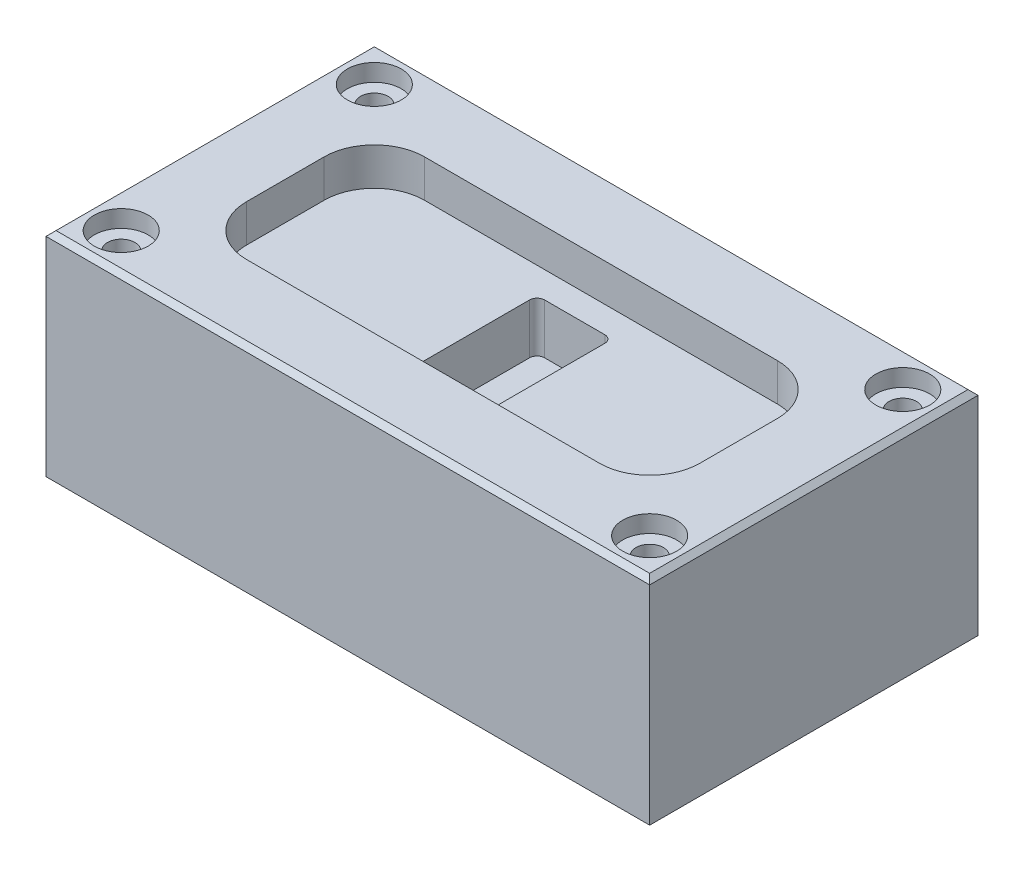
SolidWorks part; units mm, degrees
ref_plane "Front Plane" through (0, 0, 0) normal (0, 0, 1) x (1, 0, 0)
ref_plane "Top Plane" through (0, 0, 0) normal (0, 1, 0) x (1, 0, 0)
ref_plane "Right Plane" through (0, 0, 0) normal (1, 0, 0) x (0, 0, -1)
sketch "Sketch3" plane through (0, 0, 0) normal (0, 1, 0) x (1, 0, 0)
  line L1 (-120.3827, -65.4738) -> (120.3827, -65.4738)
  line L2 (-120.3827, -65.4738) -> (-120.3827, 65.4738)
  line L3 (-120.3827, 65.4738) -> (120.3827, 65.4738)
  line L4 (120.3827, -65.4738) -> (120.3827, 65.4738)
  line L5 (-120.3827, -65.4738) -> (120.3827, 65.4738) construction
  line L6 (-120.3827, 65.4738) -> (120.3827, -65.4738) construction
  point P0 (0, 0)
extrude "Boss-Extrude2" add sketch "Sketch3" along normal blind 85
sketch "Sketch4" plane through (0, 85, 0) normal (0, 1, 0) x (1, 0, 0)
  line L8 (90.3827, -35.4738) -> (90.3827, 35.4738)
  line L9 (90.3827, 35.4738) -> (-90.3827, 35.4738)
  line L10 (-90.3827, 35.4738) -> (-90.3827, -35.4738)
  line L11 (-90.3827, -35.4738) -> (90.3827, -35.4738)
  line L12 (90.3827, -35.4738) -> (90.3827, 35.4738)
  line L13 (90.3827, 35.4738) -> (-90.3827, 35.4738)
  line L14 (-90.3827, 35.4738) -> (-90.3827, -35.4738)
  line L15 (-90.3827, -35.4738) -> (90.3827, -35.4738)
  dimension "D1" = 30
extrude "Cut-Extrude1" cut sketch "Sketch4" against normal blind 15
sketch "Sketch5" plane through (0, 85, 0) normal (0, 1, 0) x (1, 0, 0)
  line L8 (105.3827, -50.4738) -> (105.3827, 50.4738)
  line L9 (105.3827, 50.4738) -> (-105.3827, 50.4738)
  line L10 (-105.3827, 50.4738) -> (-105.3827, -50.4738)
  line L11 (-105.3827, -50.4738) -> (105.3827, -50.4738)
  line L12 (105.3827, -50.4738) -> (105.3827, 50.4738) construction
  line L13 (105.3827, 50.4738) -> (-105.3827, 50.4738) construction
  line L14 (-105.3827, 50.4738) -> (-105.3827, -50.4738) construction
  line L15 (-105.3827, -50.4738) -> (105.3827, -50.4738) construction
  dimension "D1" = 15
hole_wizard "CBORE for M10 Hex Head Bolt1" positions "3DSketch2" profile "Sketch6" counterbore size "M10" standard "ANSI Metric"
sketch3d "3DSketch2"
  point P0 (-105.3827, 85, -50.4738)
  point P3 (-105.3827, 85, 50.4738)
  point P6 (105.3827, 85, -50.4738)
  point P9 (105.3827, 85, 50.4738)
sketch "Sketch6" plane through (-105.3827, 85, -50.4738) normal (1, 0, 0) x (0, 0, 1)
  line L0 (0, 0) -> (0, 23.3047)
  line L1 (0, 23.3047) -> (5.5, 20)
  line L2 (5.5, 20) -> (5.5, 6.85)
  line L3 (5.5, 6.85) -> (10.74, 6.85)
  line L4 (10.74, 6.85) -> (10.74, 0)
  line L5 (10.74, 0) -> (0, 0)
  line L10 (0, 23.3047) -> (-5.5, 20) construction
  line L11 (0, -6.35) -> (0, 107.95) construction
  dimension "Hole Dia." = 11
  dimension "Hole Depth" = 20
  dimension "C'Bore Dia." = 21.48
  dimension "C'Bore Depth" = 6.85
  dimension "Drill Angle" = 118
fillet "Fillet1" radius 20 4 edges at (-90.3827, 77.5, 35.4738) (90.3827, 77.5, 35.4738) (90.3827, 77.5, -35.4738) (-90.3827, 77.5, -35.4738)
chamfer "Chamfer1" distance 2 angle 45 4 edges at (0, 85, 65.4738) (120.3827, 85, 0) (0, 85, -65.4738) (-120.3827, 85, 0)
sketch "Sketch7" plane through (0, 70, 0) normal (0, 1, 0) x (1, 0, 0)
  line L1 (-12, -25) -> (12, -25)
  line L2 (-15, -22) -> (-15, 22)
  line L3 (-12, 25) -> (12, 25)
  line L4 (15, -22) -> (15, 22)
  line L5 (-15, -25) -> (15, 25) construction
  line L6 (-15, 25) -> (15, -25) construction
  arc A0 (-12, -25) -> (-15, -22) centre (-12, -22) cw
  arc A1 (12, -25) -> (15, -22) centre (12, -22) ccw
  arc A2 (12, 25) -> (15, 22) centre (12, 22) cw
  arc A3 (-15, 22) -> (-12, 25) centre (-12, 22) cw
  point P0 (0, 0)
  dimension "D3" = 3
  dimension "D1" = 30
  dimension "D2" = 50
extrude "Cut-Extrude2" cut sketch "Sketch7" against normal blind 20
